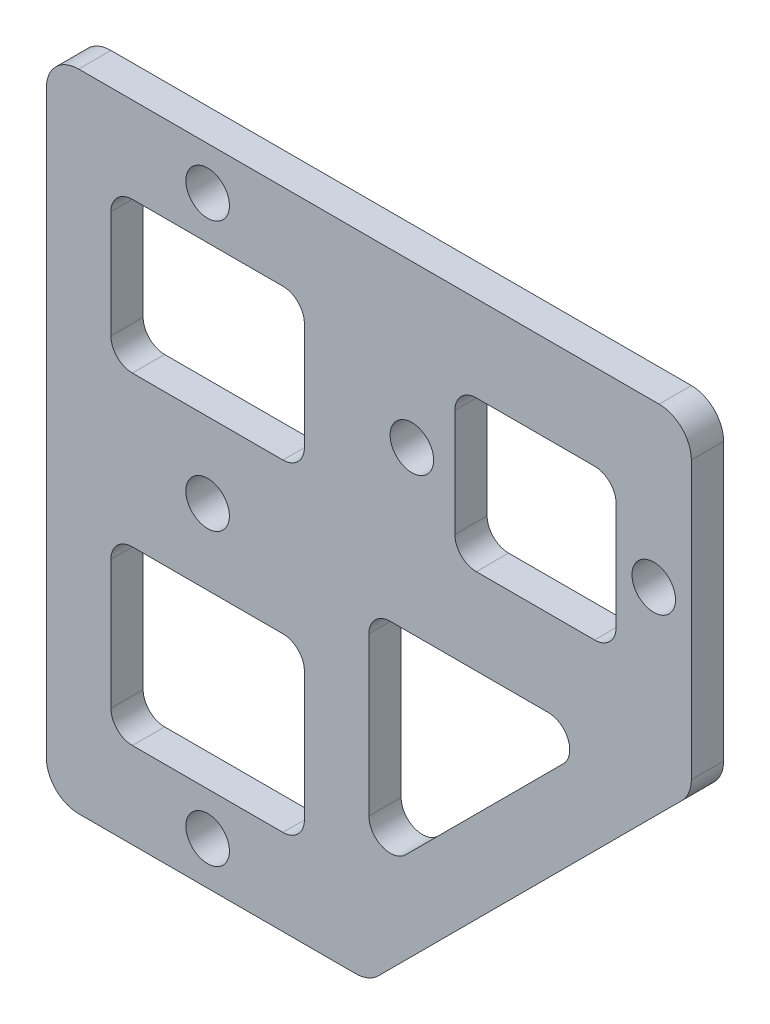
SolidWorks part; units mm, degrees
material "Thornel Mat VMA"
ref_plane "前视基准面" through (0, 0, 0) normal (0, 0, 1) x (1, 0, 0)
ref_plane "上视基准面" through (0, 0, 0) normal (0, 1, 0) x (1, 0, 0)
ref_plane "右视基准面" through (0, 0, 0) normal (1, 0, 0) x (0, 0, -1)
other "Configuration Table"
sketch "草图1" plane through (0, 0, 0) normal (0, 0, 1) x (1, 0, 0)
  line L0 (0, 0) -> (60, 0)
  line L1 (60, 0) -> (60, -30)
  line L2 (60, -30) -> (30, -60)
  line L3 (30, -60) -> (0, -60)
  line L4 (0, -60) -> (0, 0)
  dimension "D1" = 30
  dimension "D2" = 30
  dimension "D3" = 30
extrude "凸台-拉伸1" add sketch "草图1" along normal blind 3
sketch "草图2" plane through (0, 0, 3) normal (0, 0, 1) x (1, 0, 0)
  line L0 (30, -51.5147) -> (30, -30)
  line L1 (6, -22) -> (24, -22)
  line L2 (6, -22) -> (6, -8)
  line L3 (6, -8) -> (24, -8)
  line L4 (24, -22) -> (24, -8)
  line L5 (6, -22) -> (24, -8) construction
  line L6 (6, -8) -> (24, -22) construction
  line L7 (6, -52) -> (24, -52)
  line L8 (6, -52) -> (6, -36)
  line L9 (6, -36) -> (24, -36)
  line L10 (24, -52) -> (24, -36)
  line L11 (6, -52) -> (24, -36) construction
  line L12 (6, -36) -> (24, -52) construction
  line L13 (30, -30) -> (51.5147, -30)
  line L14 (51.5147, -30) -> (30, -51.5147)
  line L15 (30, -60) -> (60, -30) construction
  line L16 (60, -15) -> (0, -15) construction
  line L17 (38, -22) -> (53, -22)
  line L18 (38, -22) -> (38, -8)
  line L19 (38, -8) -> (53, -8)
  line L20 (53, -22) -> (53, -8)
  line L21 (38, -22) -> (53, -8) construction
  line L22 (38, -8) -> (53, -22) construction
  line L23 (60, -30) -> (60, 0) construction
  line L24 (0, 0) -> (0, -60) construction
  line L25 (15, -60) -> (15, -44) construction
  line L26 (0, -60) -> (30, -60) construction
  line L27 (60, 0) -> (0, 0) construction
  point P0 (15, -15)
  point P5 (15, -44)
  point P17 (45.5, -15)
  dimension "D1" = 6
  dimension "D2" = 18
  dimension "D3" = 16
  dimension "D4" = 8
  dimension "D5" = 8
  dimension "D6" = 7
  dimension "D7" = 15
extrude "切除-拉伸1" cut sketch "草图2" against normal blind 10
fillet "圆角1" radius 2 15 edges at (24, -22, 1.5) (6, -22, 1.5) (6, -8, 1.5) (24, -8, 1.5) (24, -52, 1.5) (6, -36, 1.5) (24, -36, 1.5) (30, -51.5147, 1.5) (30, -30, 1.5) (51.5147, -30, 1.5) (53, -22, 1.5) (38, -22, 1.5) (38, -8, 1.5) (53, -8, 1.5) (6, -52, 1.5)
fillet "圆角2" radius 3 5 edges at (0, 0, 1.5) (60, -30, 1.5) (30, -60, 1.5) (0, -60, 1.5) (60, 0, 1.5)
sketch "草图4" plane through (0, 0, 3) normal (0, 0, 1) x (1, 0, 0)
  line L0 (15, -22) -> (15, -36) construction
  line L1 (3, -60) -> (28.7574, -60) construction
  line L2 (15, -52) -> (15, -60) construction
  line L3 (8, -52) -> (22, -52) construction
  line L4 (8, -22) -> (22, -22) construction
  line L5 (22, -36) -> (8, -36) construction
  line L7 (15, -8) -> (15, 0) construction
  line L8 (22, -8) -> (8, -8) construction
  line L9 (57, 0) -> (3, 0) construction
  circle A0 centre (15, -29) radius 2.025
  circle A1 centre (15, -56) radius 2.025
  circle A2 centre (15, -4) radius 2.025
  point P13 (15, -56)
  dimension "D1" = 4.05
extrude "切除-拉伸2" cut sketch "草图4" against normal blind 10
sketch "草图5" plane through (0, 0, 3) normal (0, 0, 1) x (1, 0, 0)
  line L4 (53, -15) -> (60, -15) construction
  line L5 (53, -20) -> (53, -10) construction
  line L6 (60, -28.7574) -> (60, -3) construction
  line L8 (38, -10) -> (38, -20) construction
  circle A0 centre (34, -15) radius 2.025
  circle A1 centre (56.5, -15) radius 2.025
  point P14 (38, -15)
  dimension "D1" = 4.05
  dimension "D2" = 4
extrude "切除-拉伸3" cut sketch "草图5" against normal blind 10
